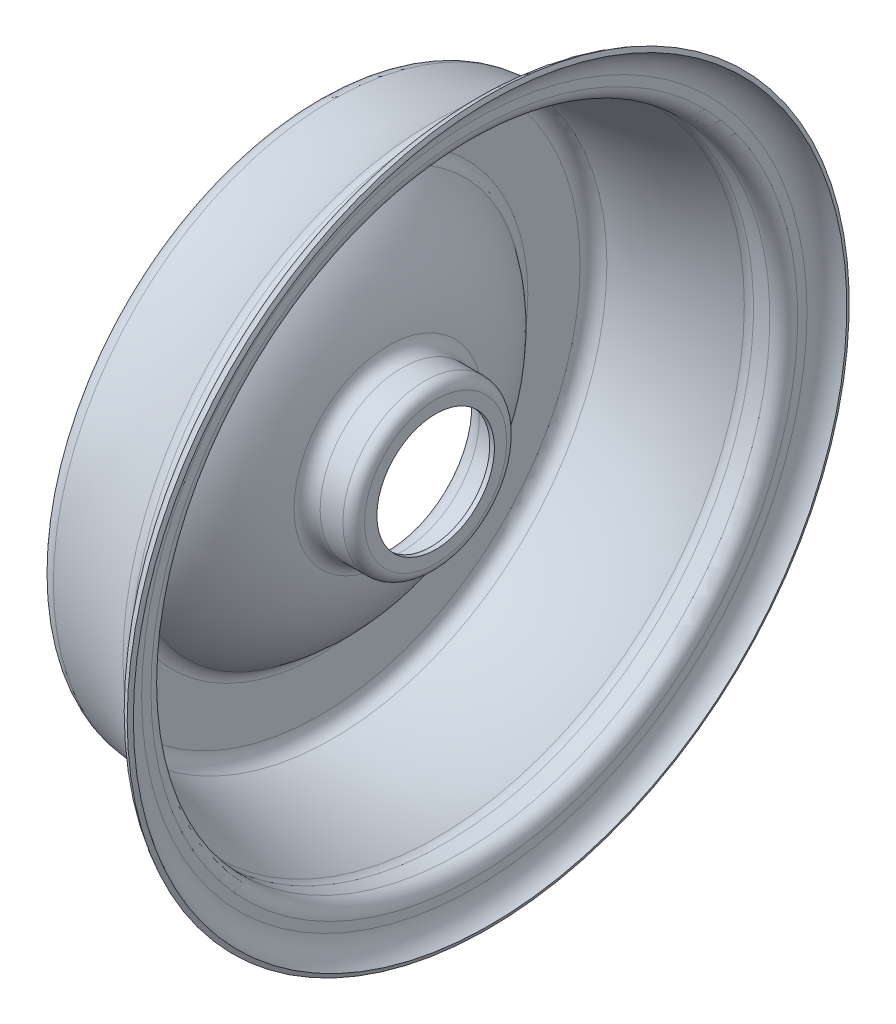
SolidWorks part; units mm, degrees
material "Plain Carbon Steel"
ref_plane "Front Plane" through (0, 0, 0) normal (0, 0, 1) x (1, 0, 0)
ref_plane "Top Plane" through (0, 0, 0) normal (0, 1, 0) x (1, 0, 0)
ref_plane "Right Plane" through (0, 0, 0) normal (1, 0, 0) x (0, 0, -1)
sketch "Sketch1" plane through (0, 0, 0) normal (0, 0, 1) x (1, 0, 0)
  line L0 (37.5, 19) -> (37.5, 23)
  line L1 (35.5, 25) -> (28.1462, 25)
  line L2 (0, 67.3202) -> (0, 84.2232)
  line L3 (41.7037, 101.6) -> (47, 101.6)
  line L4 (0, 0) -> (28.0725, 0) construction
  line L5 (50, 104.6) -> (50, 107.6)
  line L6 (39, 19) -> (39, 23)
  line L7 (35.5, 26.5) -> (28.1462, 26.5)
  line L8 (1.5, 67.3202) -> (1.5, 84.2232)
  line L9 (41.7037, 100.1) -> (47, 100.1)
  line L10 (51.5, 104.6) -> (51.5, 107.6)
  line L11 (56, 116.7652) -> (56.6, 115.3904)
  line L12 (39, 19) -> (37.5, 19)
  arc A0 (22.1878, 30.2948) -> (2.6445, 62.3462) centre (-22.55, 25) ccw
  arc A1 (5.5543, 90.2066) -> (38.6056, 100.7382) centre (0, 164.7655) ccw
  arc A2 (50, 107.6) -> (56, 116.7652) centre (60, 107.6) cw
  arc A3 (47, 101.6) -> (50, 104.6) centre (47, 104.6) ccw
  arc A4 (37.5, 23) -> (35.5, 25) centre (35.5, 23) ccw
  arc A5 (38.6056, 100.7382) -> (41.7037, 101.6) centre (41.7037, 95.6) cw
  arc A6 (0, 84.2232) -> (5.5543, 90.2066) centre (6, 84.2232) cw
  arc A7 (2.6445, 62.3462) -> (0, 67.3202) centre (6, 67.3202) cw
  arc A8 (28.1462, 25) -> (22.1878, 30.2948) centre (28.1462, 31) cw
  arc A9 (39, 23) -> (35.5, 26.5) centre (35.5, 23) ccw
  arc A10 (28.1462, 26.5) -> (23.6774, 30.4711) centre (28.1462, 31) cw
  arc A11 (23.6774, 30.4711) -> (3.4833, 63.5897) centre (-22.55, 25) ccw
  arc A12 (3.4833, 63.5897) -> (1.5, 67.3202) centre (6, 67.3202) cw
  arc A13 (1.5, 84.2232) -> (5.6657, 88.7107) centre (6, 84.2232) cw
  arc A14 (5.6657, 88.7107) -> (39.3801, 99.4537) centre (0, 164.7655) ccw
  arc A15 (39.3801, 99.4537) -> (41.7037, 100.1) centre (41.7037, 95.6) cw
  arc A16 (47, 100.1) -> (51.5, 104.6) centre (47, 104.6) ccw
  arc A17 (51.5, 107.6) -> (56.6, 115.3904) centre (60, 107.6) cw
  point P17 (50, 101.6)
  point P20 (37.5, 25)
  point P23 (40, 101.6)
  point P26 (0, 90)
  point P29 (0, 64)
  point P32 (22.5, 25)
  dimension "D4" = 10
  dimension "D13" = 3
  dimension "D14" = 2
  dimension "D15" = 6
  dimension "D1" = 25
  dimension "D2" = 203.2
  dimension "D3" = 50
  dimension "D5" = 6
  dimension "D6" = 6
  dimension "D7" = 10
  dimension "D8" = 180
  dimension "D9" = 37.5
  dimension "D10" = 15
  dimension "D11" = 26
  dimension "D12" = 6
  dimension "D16" = 1.5
revolve "Revolve1" add sketch "Sketch1" angle 360 about L4
